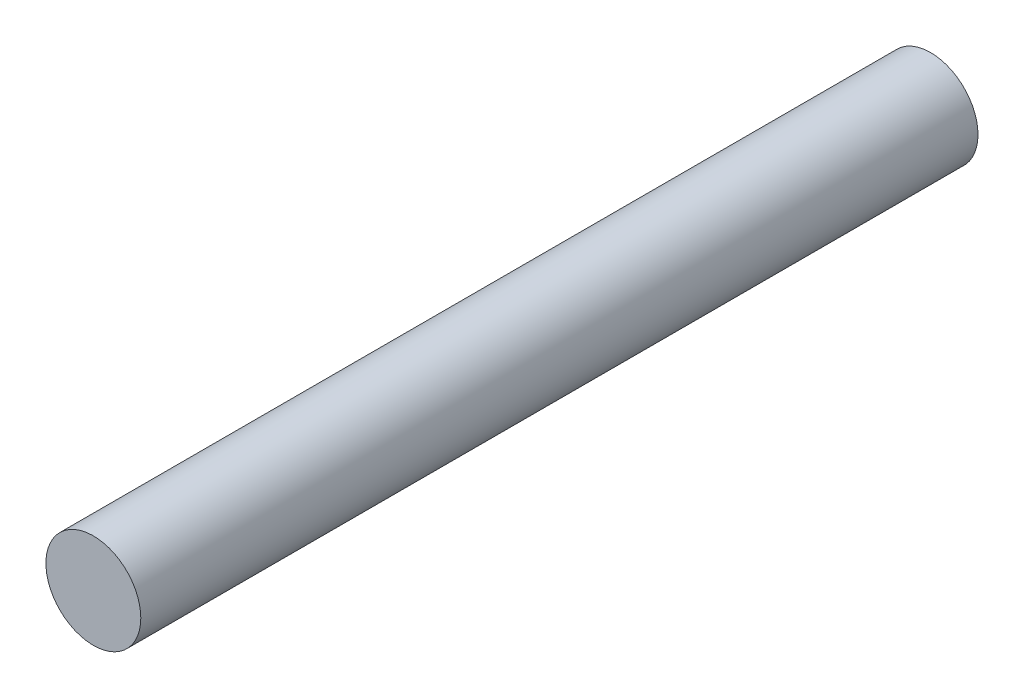
SolidWorks part; units mm, degrees
ref_plane "Front Plane" through (0, 0, 0) normal (0, 0, 1) x (1, 0, 0)
ref_plane "Top Plane" through (0, 0, 0) normal (0, 1, 0) x (1, 0, 0)
ref_plane "Right Plane" through (0, 0, 0) normal (1, 0, 0) x (0, 0, -1)
sketch "Sketch1" plane through (0, 0, 0) normal (0, 0, 1) x (1, 0, 0)
  circle A0 centre (0, 0) radius 4.25
  dimension "D1" = 8.5
extrude "Boss-Extrude1" add sketch "Sketch1" along normal blind 75
